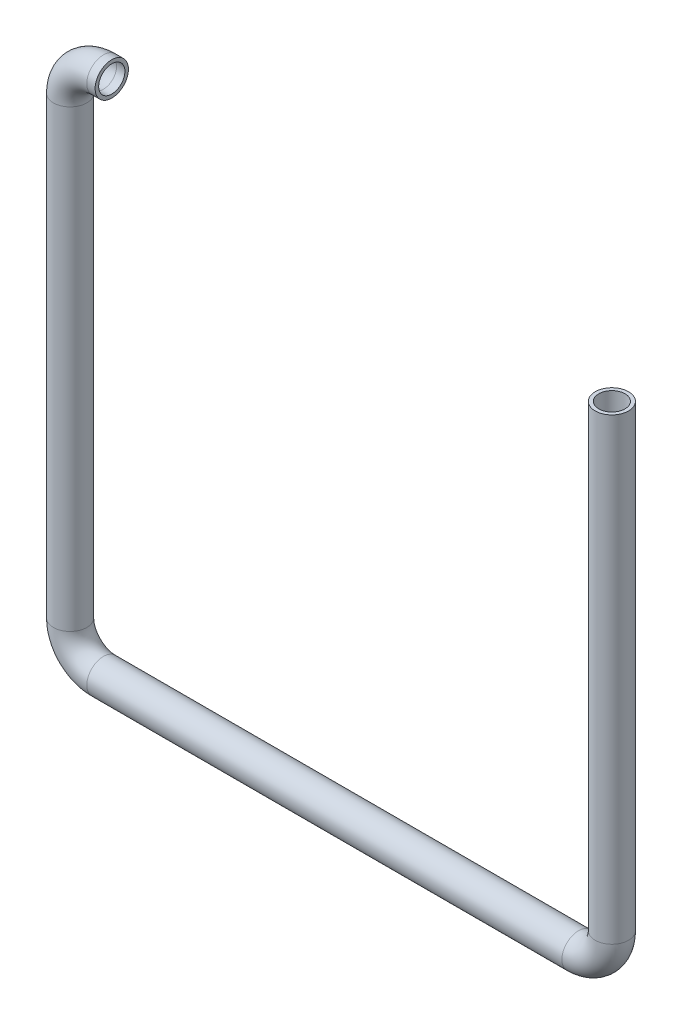
SolidWorks part; units mm, degrees
ref_plane "Front Plane" through (0, 0, 0) normal (0, 0, 1) x (1, 0, 0)
ref_plane "Top Plane" through (0, 0, 0) normal (0, 1, 0) x (1, 0, 0)
ref_plane "Right Plane" through (0, 0, 0) normal (1, 0, 0) x (0, 0, -1)
sketch "Sketch1" plane through (0, 0, 0) normal (0, 0, 1) x (1, 0, 0)
  line L0 (0, 0) -> (-2, 0)
  line L1 (-10, -8) -> (-10, -117)
  line L2 (-2, -125) -> (112, -125)
  line L3 (120, -117) -> (120, -7)
  arc A0 (-2, 0) -> (-10, -8) centre (-2, -8) ccw
  arc A1 (112, -125) -> (120, -117) centre (112, -117) ccw
  arc A2 (-10, -117) -> (-2, -125) centre (-2, -117) ccw
  point P8 (-10, 0)
  point P11 (120, -125)
  point P14 (-10, -125)
  dimension "D5" = 8
  dimension "D1" = 10
  dimension "D2" = 125
  dimension "D3" = 130
  dimension "D4" = 7
sketch "Sketch2" plane through (0, 0, 0) normal (1, 0, 0) x (0, 0, -1)
  circle A0 centre (0, 0) radius 3.15
  circle A1 centre (0, 0) radius 4
  dimension "D1" = 8
  dimension "D2" = 6.3
sweep "Sweep1" add profiles "Sketch2" path "Sketch1"
